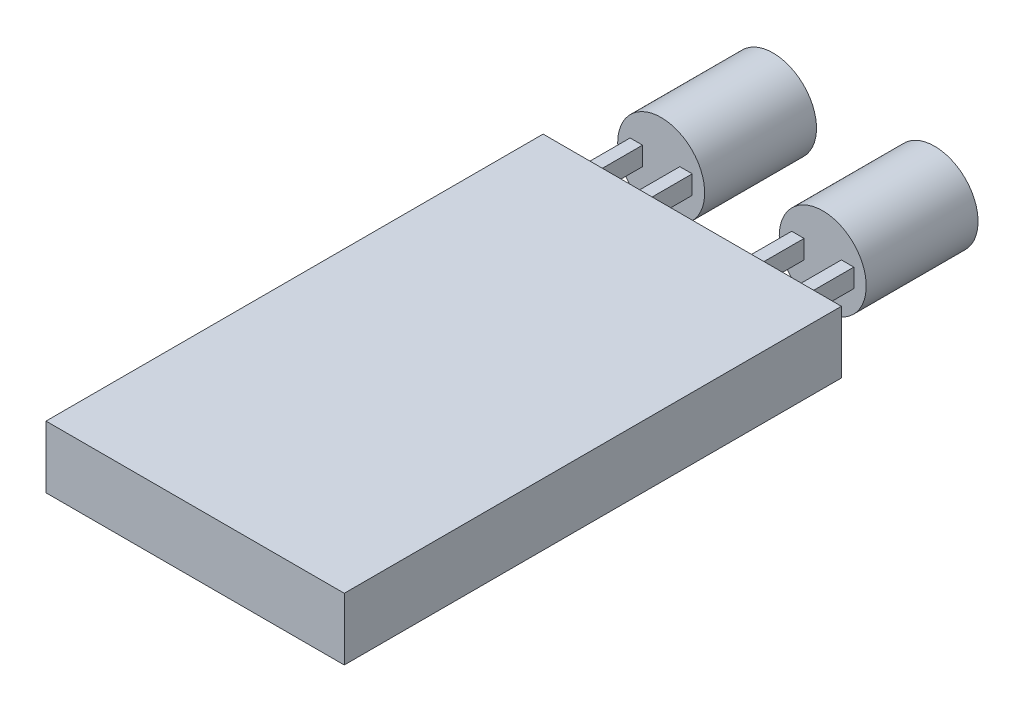
SolidWorks part; units mm, degrees
ref_plane "Front Plane" through (0, 0, 0) normal (0, 0, 1) x (1, 0, 0)
ref_plane "Top Plane" through (0, 0, 0) normal (0, 1, 0) x (1, 0, 0)
ref_plane "Right Plane" through (0, 0, 0) normal (1, 0, 0) x (0, 0, -1)
sketch "Sketch1" plane through (0, 0, 0) normal (0, 1, 0) x (1, 0, 0)
  line L1 (-24, 9.4286) -> (0, 9.4286)
  line L2 (-24, 9.4286) -> (-24, -30.5714)
  line L3 (-24, -30.5714) -> (0, -30.5714)
  line L4 (0, 9.4286) -> (0, -30.5714)
  dimension "D1" = 24
  dimension "D2" = 40
extrude "Boss-Extrude1" add sketch "Sketch1" along normal blind 5
sketch "Sketch2" plane through (0, 0, -9.4286) normal (0, 0, -1) x (-1, 0, 0)
  line L0 (0, 5) -> (0, 0) construction
  line L1 (3, 4.2295) -> (4, 4.2295)
  line L2 (3, 4.2295) -> (3, 2.7295)
  line L3 (3, 2.7295) -> (4, 2.7295)
  line L4 (4, 4.2295) -> (4, 2.7295)
  line L5 (7, 4.2295) -> (8, 4.2295)
  line L6 (7, 4.2295) -> (7, 2.7295)
  line L7 (7, 2.7295) -> (8, 2.7295)
  line L8 (8, 4.2295) -> (8, 2.7295)
  line L9 (16, 4.2295) -> (16, 2.7295)
  line L10 (16, 4.2295) -> (17, 4.2295)
  line L11 (16, 2.7295) -> (17, 2.7295)
  line L12 (17, 4.2295) -> (17, 2.7295)
  line L13 (20, 4.2295) -> (20, 2.7295)
  line L14 (20, 4.2295) -> (21, 4.2295)
  line L15 (20, 2.7295) -> (21, 2.7295)
  line L16 (21, 4.2295) -> (21, 2.7295)
  dimension "D1" = 1
  dimension "D2" = 1.5
  dimension "D3" = 1
  dimension "D4" = 1.5
  dimension "D5" = 3
  dimension "D6" = 3
  dimension "D7" = 2
extrude "Boss-Extrude2" add sketch "Sketch2" along normal blind 4
sketch "Sketch4" plane through (0, 0, -13.4286) normal (0, 0, -1) x (-1, 0, 0)
  line L0 (4, 2.7295) -> (4, 4.2295) construction
  line L1 (17, 2.7295) -> (17, 4.2295) construction
  circle A0 centre (5.5, 3.4061) radius 3.5
  circle A1 centre (18.5, 3.4061) radius 3.5
  point P4 (4, 3.4795)
  point P7 (17, 3.4795)
  dimension "D1" = 7
  dimension "D2" = 7
  dimension "D3" = 1.5
  dimension "D4" = 1.5
extrude "Boss-Extrude4" add sketch "Sketch4" along normal blind 9
